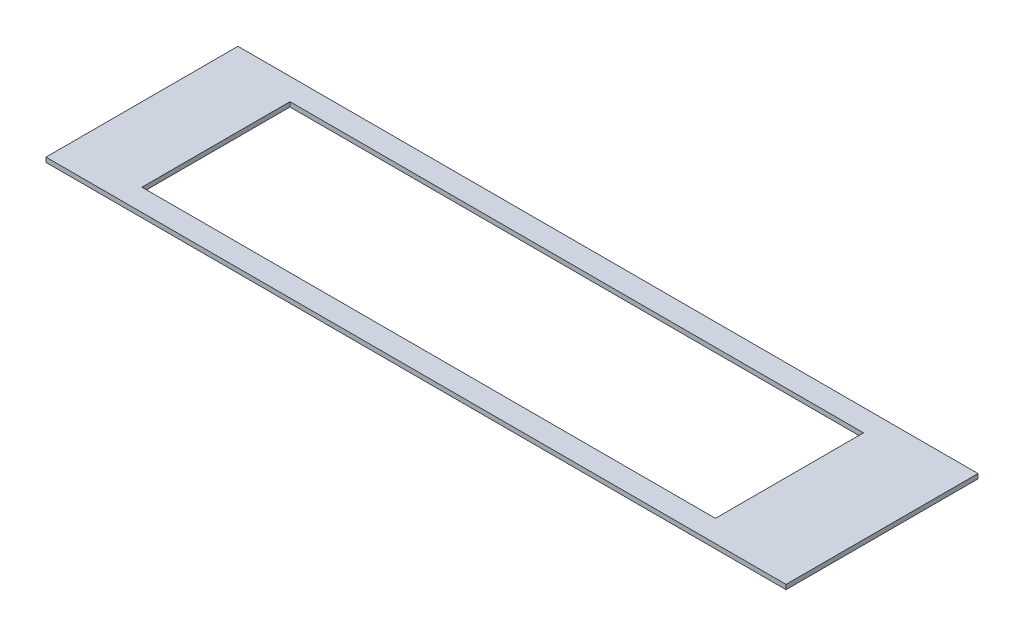
SolidWorks part; units mm, degrees
ref_plane "Front" through (0, 0, 0) normal (0, 0, 1) x (1, 0, 0)
ref_plane "Top" through (0, 0, 0) normal (0, 1, 0) x (1, 0, 0)
ref_plane "Right" through (0, 0, 0) normal (1, 0, 0) x (0, 0, -1)
sketch "Sketch1" plane through (0, 0, 0) normal (0, 1, 0) x (1, 0, 0)
  line L0 (244.475, 65.8844) -> (254, 65.8844)
  line L1 (-254, -72.3614) -> (254, -72.3614)
  line L2 (-254, -72.3614) -> (-254, 72.3614)
  line L3 (-254, 72.3614) -> (254, 72.3614)
  line L4 (254, -72.3614) -> (254, 72.3614)
  line L5 (-254, -72.3614) -> (254, 72.3614) construction
  line L6 (-254, 72.3614) -> (254, -72.3614) construction
  line L7 (-254, 72.3614) -> (244.475, 72.3614)
  line L8 (-254, 72.3614) -> (-254, 65.8844)
  line L9 (-254, 65.8844) -> (244.475, 65.8844)
  line L10 (244.475, 72.3614) -> (244.475, 65.8844)
  line L11 (-254, -72.3614) -> (244.475, -72.3614)
  line L12 (-254, -72.3614) -> (-254, -65.8844)
  line L13 (-254, -65.8844) -> (244.475, -65.8844)
  line L14 (244.475, -72.3614) -> (244.475, -65.8844)
  line L15 (-203.2, -50.8508) -> (190.5, -50.8508)
  line L16 (-203.2, -50.8508) -> (-203.2, 50.8)
  line L17 (-203.2, 50.8) -> (190.5, 50.8)
  line L18 (190.5, -50.8508) -> (190.5, 50.8)
  line L19 (244.475, -65.8844) -> (254, -65.8844)
  point P0 (0, 0)
  point P12 (0, 0)
  dimension "D1" = 144.7228
  dimension "D2" = 508
  dimension "D3" = 9.525
  dimension "D4" = 6.477
  dimension "D5" = 101.6508
  dimension "D7" = 50.8
  dimension "D8" = 63.5
  dimension "D6" = 393.7
extrude "Boss-Extrude1" add sketch "Sketch1" along normal blind 3.175 contours L14 L1 L4 L3 L10 L9 L2 L13 L18 L15 L16 L17
equation "\"D1@Sketch1\"      = 4.98025 - 0.002 + 2 * ( 0.25 + 0.016 + ( 6 / 64 ) )"
